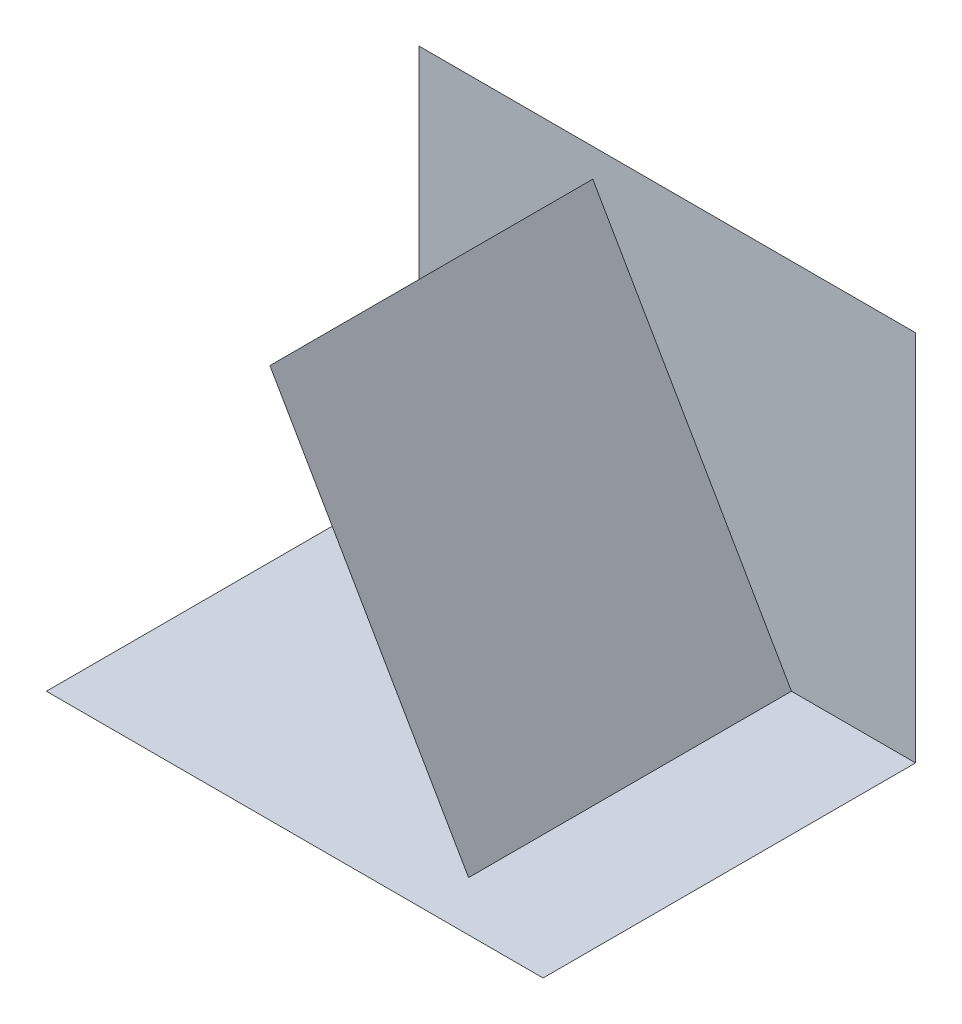
SolidWorks part; units mm, degrees
ref_plane "Front Plane" through (0, 0, 0) normal (0, 0, 1) x (1, 0, 0)
ref_plane "Top Plane" through (0, 0, 0) normal (0, 1, 0) x (1, 0, 0)
ref_plane "Right Plane" through (0, 0, 0) normal (1, 0, 0) x (0, 0, -1)
sketch "Sketch1" plane through (0, 0, 0) normal (0, 0, 1) x (1, 0, 0)
  line L1 (-100, 150) -> (100, 150)
  line L2 (-100, 150) -> (-100, 0)
  line L3 (-100, 0) -> (100, 0)
  line L4 (100, 150) -> (100, 0)
  dimension "D1" = 150
  dimension "D2" = 200
extrude "Extrude1" add sketch "Sketch1" against normal blind 0.0001
sketch "Sketch2" plane through (0, 0, 0) normal (0, 1, 0) x (1, 0, 0)
  line L1 (-100, 0) -> (100, 0)
  line L2 (-100, 0) -> (-100, -150)
  line L3 (-100, -150) -> (100, -150)
  line L4 (100, 0) -> (100, -150)
  dimension "D1" = 200
  dimension "D2" = 150
extrude "Extrude2" add sketch "Sketch2" against normal blind 0.0001
sketch "Sketch3" plane through (0, 0, 0) normal (0, 1, 0) x (-1, 0, 0)
  line L0 (-50, 0) -> (-50, 124.6665) construction
  line L1 (-100, 0) -> (100, 0) construction
  line L2 (100, 0) -> (100, 150) construction
  dimension "D1" = 150
ref_plane "Plane1" through (37.5, 21.6506, 0) normal (-0.866, -0.5, 0) x (0, 0, 1)
sketch "Sketch4" plane through (37.5, 21.6506, 0) normal (-0.866, -0.5, 0) x (0, 0, 1)
  line L1 (130, 135) -> (0, 135)
  line L2 (130, 135) -> (130, -25)
  line L3 (130, -25) -> (0, -25)
  line L4 (0, 135) -> (0, -25)
  dimension "D1" = 160
  dimension "D2" = 130
surface "Surface-Fill1" sketch "Sketch4"
